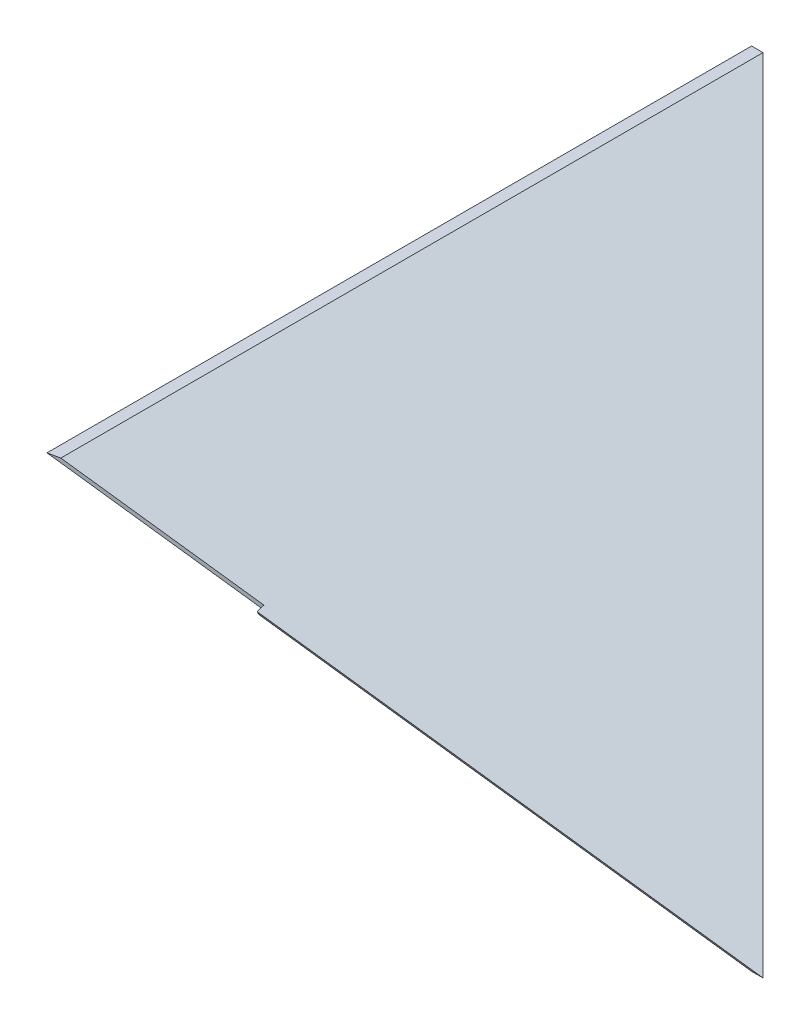
SolidWorks part; units mm, degrees
ref_plane "Front Plane" through (0, 0, 0) normal (0, 0, 1) x (1, 0, 0)
ref_plane "Top Plane" through (0, 0, 0) normal (0, 1, 0) x (1, 0, 0)
ref_plane "Right Plane" through (0, 0, 0) normal (1, 0, 0) x (0, 0, -1)
sketch "Sketch1" plane through (0, 0, 0) normal (1, 0, 0) x (0, 0, -1)
  line L0 (0, 0) -> (-197.18, 0)
  line L1 (-197.18, 0) -> (-162.9401, -59.3053)
  line L2 (-162.9401, -59.3053) -> (0, 0)
  dimension "D1" = 20
  dimension "D2" = 60
  dimension "D3" = 197.18
extrude "Boss-Extrude1" add sketch "Sketch1" along normal blind 304.8
sketch "Sketch2" plane through (0, 0, 0) normal (0, 0, 1) x (1, 0, 0)
  line L0 (0, 0) -> (162.9401, -59.3053)
  line L1 (304.8, -59.3053) -> (0, -59.3053) construction
  line L3 (166.1151, -59.3053) -> (3.175, 0)
  line L4 (304.8, 0) -> (0, 0) construction
  line L5 (152.4, 0) -> (152.4, 50000) construction
  line L11 (0, 0) -> (0, -59.3053)
  line L12 (0, -59.3053) -> (162.9401, -59.3053)
  line L13 (3.175, 0) -> (304.8, 0)
  line L14 (304.8, 0) -> (304.8, -59.3053)
  line L15 (304.8, -59.3053) -> (166.1151, -59.3053)
  point P10 (152.4, 0)
  dimension "D1" = 3.175
  dimension "D2" = 20
extrude "Cut-Extrude1" cut sketch "Sketch2" against normal through all and the other way through all
sketch "Sketch4" plane through (0, 0, 0) normal (0, 1, 0) x (1, 0, 0)
  line L0 (50.2039, -187.2974) -> (49.7142, -184.9671)
  line L5 (166.1151, -162.9401) -> (3.175, -197.18) construction
  line L6 (49.7142, -184.9671) -> (0, -195.4139)
  line L7 (0, 0) -> (0, -197.18) construction
  line L8 (0, -195.4139) -> (0, -197.18)
  line L9 (0, -197.18) -> (3.175, -197.18)
  line L10 (3.175, -197.18) -> (50.2039, -187.2974)
  dimension "D1" = 2.3813
  dimension "D2" = 50.8
extrude "Cut-Extrude4" cut sketch "Sketch4" against normal through all
